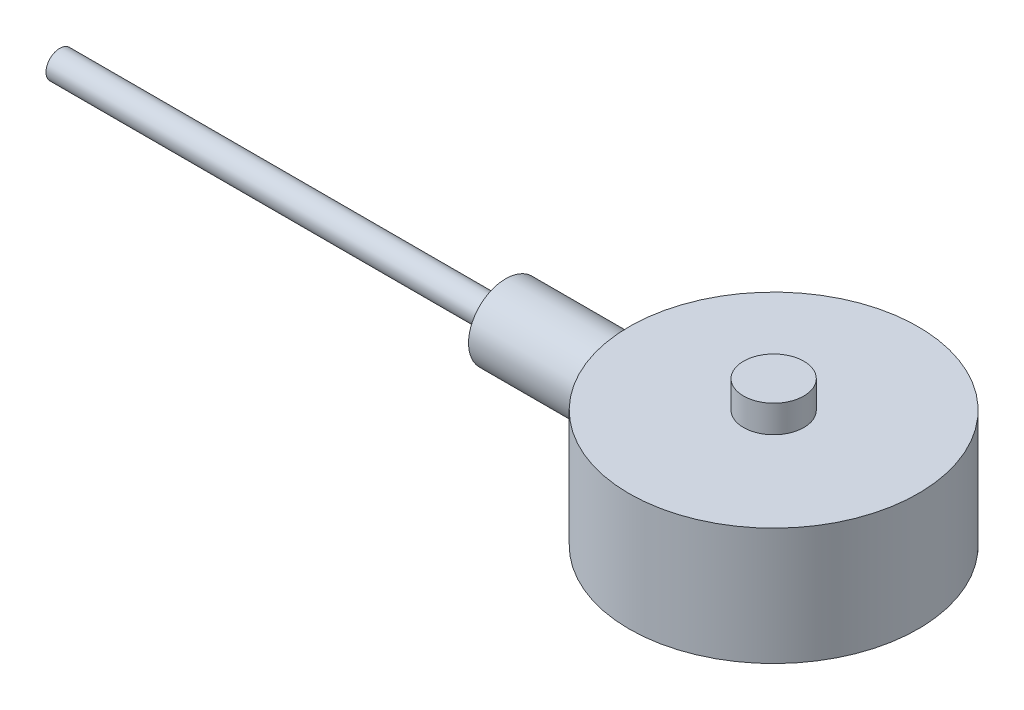
SolidWorks part; units mm, degrees
ref_plane "Front Plane" through (0, 0, 0) normal (0, 0, 1) x (1, 0, 0)
ref_plane "Top Plane" through (0, 0, 0) normal (0, 1, 0) x (1, 0, 0)
ref_plane "Right Plane" through (0, 0, 0) normal (1, 0, 0) x (0, 0, -1)
sketch "Sketch1" plane through (0, 0, 0) normal (0, 1, 0) x (1, 0, 0)
  circle A0 centre (0, 0) radius 25.4
  dimension "D1" = 50.8
extrude "base" add sketch "Sketch1" along normal blind 20.6
sketch "Sketch2" plane through (0, 20.6, 0) normal (0, 1, 0) x (1, 0, 0)
  circle A0 centre (0, 0) radius 5.3
  dimension "D1" = 10.6
extrude "button" add sketch "Sketch2" along normal blind 4.8
sketch "Sketch3" plane through (0, 0, 0) normal (0, 0, 1) x (1, 0, 0)
  line L0 (-25.0755, 10.5279) -> (-125.419, 10.5279)
  line L1 (-47.0755, 17.0607) -> (-25.0755, 17.0607)
  line L3 (-47.0755, 17.0607) -> (-47.0755, 12.9434)
  line L4 (-25.0755, 10.5279) -> (-25.0755, 17.0607) construction
  line L5 (-47.0755, 12.9434) -> (-125.419, 12.9434)
  line L6 (-125.419, 12.9434) -> (-125.419, 10.5279)
  line L9 (-19.5225, 17.0607) -> (-19.5225, 10.5279)
  line L10 (-19.5225, 10.5279) -> (-25.0755, 10.5279)
  line L13 (-19.5225, 17.0607) -> (-25.0755, 17.0607)
  dimension "D1" = 22
revolve "cable" add sketch "Sketch3" angle 360 about L0
sketch "Sketch4" plane through (0, 0, 0) normal (0, -1, 0) x (1, 0, 0)
  line L0 (0, 0) -> (25.4, 0) construction
  line L1 (0, 0) -> (19.771, 8.1894) construction
  circle A0 centre (0, 0) radius 25.4 construction
  point P0 (19.771, 8.1894)
  point P7 (19.771, -8.1894)
  point P11 (8.1894, -19.771)
  point P12 (-8.1894, -19.771)
  point P13 (-19.771, -8.1894)
  point P14 (-19.771, 8.1894)
  point P15 (-8.1894, 19.771)
  point P16 (8.1894, 19.771)
  point P17 (0, 0)
  dimension "D1" = 21.4
  dimension "D2" = 22.5
  dimension "D3" = 8
hole_wizard "Ø5.0mm Dowel Hole1" positions "3DSketch1" profile "Sketch5" hole size "Ø5.0" standard "ANSI Metric"
sketch3d "3DSketch1"
  point P0 (-19.771, 0, 8.1894)
  point P3 (-8.1894, 0, 19.771)
  point P6 (8.1894, 0, 19.771)
  point P9 (19.771, 0, 8.1894)
  point P12 (19.771, 0, -8.1894)
  point P15 (8.1894, 0, -19.771)
  point P18 (-8.1894, 0, -19.771)
  point P21 (-19.771, 0, -8.1894)
sketch "Sketch5" plane through (-19.771, 0, 8.1894) normal (1, 0, 0) x (0, 0, -1)
  line L0 (0, 0) -> (0, 11.7022)
  line L1 (0, 11.7022) -> (2.5, 10.2)
  line L2 (2.5, 10.2) -> (2.5, 0)
  line L5 (2.5, 0) -> (0, 0)
  line L10 (0, 11.7022) -> (-2.5, 10.2) construction
  line L11 (0, -6.35) -> (0, 107.95) construction
  dimension "Hole Dia." = 5
  dimension "Hole Depth" = 10.2
  dimension "Drill Angle" = 118
cosmetic thread "Cosmetic Thread1" parameters "D1"=5, "D2"=6.35
cosmetic thread "Cosmetic Thread2" parameters "D1"=5, "D2"=6.35
cosmetic thread "Cosmetic Thread3" parameters "D1"=5, "D2"=6.35
cosmetic thread "Cosmetic Thread4" parameters "D1"=5, "D2"=6.35
cosmetic thread "Cosmetic Thread5" parameters "D1"=5, "D2"=6.35
cosmetic thread "Cosmetic Thread6" parameters "D1"=5, "D2"=6.35
cosmetic thread "Cosmetic Thread7" parameters "D1"=5, "D2"=6.35
cosmetic thread "Cosmetic Thread8" parameters "D1"=5, "D2"=6.35
